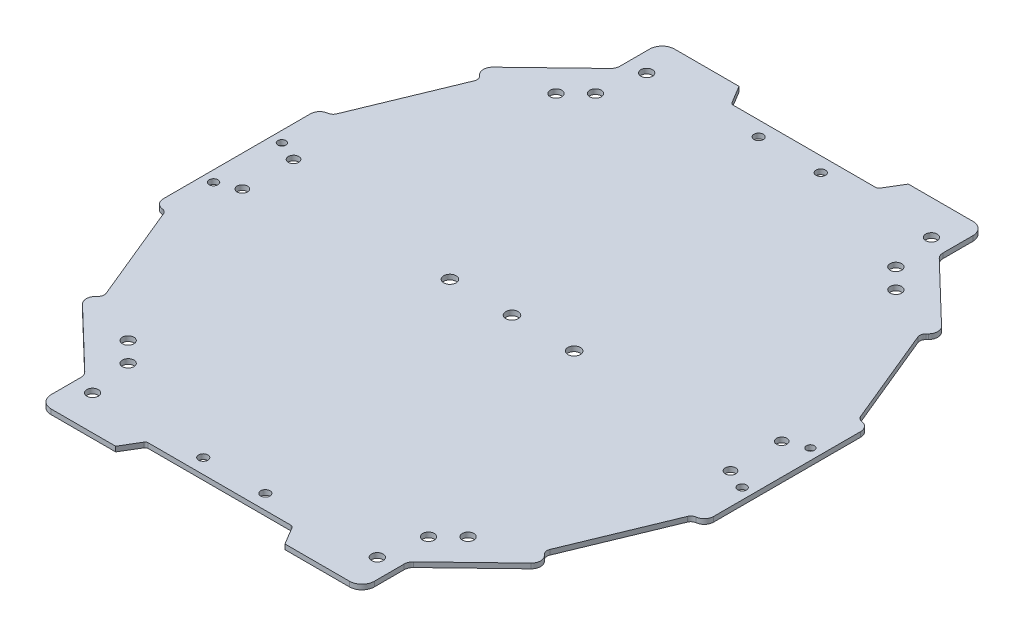
SolidWorks part; units mm, degrees
ref_plane "Front Plane" through (0, 0, 0) normal (0, 0, 1) x (1, 0, 0)
ref_plane "Top Plane" through (0, 0, 0) normal (0, 1, 0) x (1, 0, 0)
ref_plane "Right Plane" through (0, 0, 0) normal (1, 0, 0) x (0, 0, -1)
ref_plane "Plane1"
sketch "Sketch1" plane through (0, 0, 0) normal (0, 1, 0) x (-1, 0, 0)
  line L0 (74.0875, 321.0883) -> (70.3692, 327.2855)
  line L1 (70.3692, 327.2855) -> (45.5805, 327.2855)
  line L2 (45.5805, 327.2855) -> (45.5805, 312.4122)
  line L3 (45.5805, 312.4122) -> (23.246, 290.9343)
  line L4 (23.246, 290.9343) -> (26.6825, 287.3608)
  line L5 (26.6825, 287.3608) -> (12.7354, 253.539)
  line L6 (12.7354, 253.539) -> (9.0171, 253.539)
  line L7 (9.0171, 253.539) -> (9.0171, 226.8911)
  line L8 (9.0171, 226.8911) -> (9.0171, 200.2432)
  line L9 (9.0171, 200.2432) -> (12.7354, 200.2432)
  line L10 (12.7354, 200.2432) -> (26.6825, 166.4214)
  line L11 (26.6825, 166.4214) -> (23.246, 162.8479)
  line L12 (23.246, 162.8479) -> (45.5805, 141.37)
  line L13 (45.5805, 141.37) -> (45.5805, 126.4967)
  line L14 (45.5805, 126.4967) -> (70.3692, 126.4967)
  line L15 (70.3692, 126.4967) -> (74.0875, 132.6939)
  line L16 (74.0875, 132.6939) -> (97.6368, 132.6939)
  line L17 (97.6368, 132.6939) -> (121.1861, 132.6939)
  line L18 (121.1861, 132.6939) -> (124.9044, 126.4967)
  line L19 (124.9044, 126.4967) -> (149.6932, 126.4967)
  line L20 (149.6932, 126.4967) -> (149.6932, 141.37)
  line L21 (149.6932, 141.37) -> (172.0276, 162.8479)
  line L22 (172.0276, 162.8479) -> (168.5911, 166.4214)
  line L23 (168.5911, 166.4214) -> (182.5382, 200.2432)
  line L24 (182.5382, 200.2432) -> (186.2565, 200.2432)
  line L25 (186.2565, 200.2432) -> (186.2565, 226.8911)
  line L26 (186.2565, 226.8911) -> (186.2565, 253.539)
  line L27 (186.2565, 253.539) -> (182.5382, 253.539)
  line L28 (182.5382, 253.539) -> (168.5911, 287.3608)
  line L29 (168.5911, 287.3608) -> (172.0276, 290.9343)
  line L30 (172.0276, 290.9343) -> (149.6932, 312.4122)
  line L31 (149.6932, 312.4122) -> (149.6932, 327.2855)
  line L32 (149.6932, 327.2855) -> (124.9044, 327.2855)
  line L33 (124.9044, 327.2855) -> (121.1861, 321.0883)
  line L34 (121.1861, 321.0883) -> (97.6368, 321.0883)
  line L35 (97.6368, 321.0883) -> (74.0875, 321.0883)
  line L36 (97.6368, 132.6939) -> (97.6368, 321.0883) construction
  line L37 (9.0171, 226.8911) -> (186.2565, 226.8911) construction
  line L38 (67.6368, 256.8911) -> (127.6368, 196.8911) construction
  line L39 (127.6368, 256.8911) -> (67.6368, 196.8911) construction
  line L40 (42.8881, 295.782) -> (49.2662, 302.1601) construction
  line L41 (146.0075, 302.1601) -> (152.3856, 295.782) construction
  line L42 (49.2662, 151.6221) -> (42.8881, 158.0002) construction
  line L43 (146.0075, 151.6221) -> (152.3856, 158.0002) construction
  line L44 (12.5171, 237.8911) -> (12.5171, 215.8911) construction
  line L45 (19.0171, 218.6411) -> (19.0171, 235.1411) construction
  line L46 (107.6368, 316.3383) -> (87.6368, 316.3383) construction
  line L126 (176.3908, 226.8911) -> (176.3908, 225.1916)
  circle A1 centre (49.2662, 151.6221) radius 1.8592
  circle A5 centre (117.6368, 226.8911) radius 2
  circle A6 centre (77.6368, 226.8911) radius 2
  circle A7 centre (97.6368, 226.8911) radius 2
  circle A8 centre (12.5171, 215.8911) radius 1.2889
  circle A9 centre (12.5171, 237.8911) radius 1.4072
  circle A10 centre (107.6368, 316.3383) radius 1.5
  circle A11 centre (87.6368, 316.3383) radius 1.5
  circle A12 centre (87.6368, 137.4439) radius 1.5
  circle A13 centre (107.6368, 137.4439) radius 1.5
  circle A14 centre (182.7565, 215.8911) radius 1.2889
  circle A15 centre (182.7565, 237.8911) radius 1.4072
  circle A16 centre (176.2565, 235.1411) radius 1.6732
  circle A17 centre (176.2565, 218.6411) radius 1.6732
  circle A22 centre (51.7777, 316.1305) radius 1.8592
  circle A23 centre (49.2662, 302.1601) radius 1.8592
  circle A24 centre (19.0171, 235.1411) radius 1.6732
  circle A27 centre (143.496, 137.6517) radius 1.8592
  circle A28 centre (146.0075, 151.6221) radius 1.8592
  circle A30 centre (143.496, 316.1305) radius 1.8592
  circle A54 centre (146.0075, 302.1601) radius 1.8592
  circle A74 centre (19.0171, 218.6411) radius 1.6732
  circle A77 centre (51.7777, 137.6517) radius 1.8592
  circle A82 centre (42.8881, 158.0002) radius 1.8592
  circle A86 centre (152.3856, 295.782) radius 1.8592
  circle A87 centre (42.8881, 295.782) radius 1.8592
  circle A91 centre (152.3856, 158.0002) radius 1.8592
  point P36 (19.0171, 226.8911)
  point P43 (97.6368, 316.3383)
  point P56 (12.5171, 226.8911)
  dimension "D1" = 30
  dimension "D11" = 20
  dimension "D14" = 40
  dimension "D28" = 6.1972
  dimension "D2" = 30
  dimension "D3" = 30
  dimension "D4" = 30
  dimension "D5" = 10
  dimension "D6" = 16.5
  dimension "D7" = 30
  dimension "D8" = 30
  dimension "D9" = 30
  dimension "D10" = 30
  dimension "D12" = 4.75
  dimension "D15" = 20
  dimension "D16" = 9.02
  dimension "D17" = 9.02
  dimension "D18" = 9.02
  dimension "D19" = 9.02
  dimension "D20" = 10
  dimension "D21" = 10
  dimension "D22" = 10
  dimension "D23" = 10
  dimension "D24" = 45
  dimension "D25" = 45
  dimension "D26" = 45
  dimension "D27" = 45
  dimension "D29" = 3.5
  dimension "D30" = 22
extrude "Extrusion1" add sketch "Sketch1" along normal blind 1.6
fillet "Fillet1" radius 1 4 edges at (-121.1861, 0.8, 132.6939) (-74.0875, 0.8, 132.6939) (-74.0875, 0.8, 321.0883) (-121.1861, 0.8, 321.0883)
fillet "Fillet2" radius 4 4 edges at (-149.6932, 0.8, 126.4967) (-45.5805, 0.8, 126.4967) (-149.6932, 0.8, 327.2855) (-45.5805, 0.8, 327.2855)
fillet "Fillet3" radius 3 4 edges at (-149.6932, 0.8, 141.37) (-45.5805, 0.8, 141.37) (-45.5805, 0.8, 312.4122) (-149.6932, 0.8, 312.4122)
fillet "Fillet4" radius 3 1 edges at (-172.0276, 0.8, 290.9343)
fillet "Fillet5" radius 2 1 edges at (-168.5911, 0.8, 287.3608)
fillet "Fillet6" radius 2 1 edges at (-26.6825, 0.8, 287.3608)
fillet "Fillet7" radius 3 1 edges at (-23.246, 0.8, 290.9343)
fillet "Fillet8" radius 3 2 edges at (-172.0276, 0.8, 162.8479) (-23.246, 0.8, 162.8479)
fillet "Fillet9" radius 2 2 edges at (-26.6825, 0.8, 166.4214) (-168.5911, 0.8, 166.4214)
fillet "Fillet10" radius 2 4 edges at (-12.7354, 0.8, 200.2432) (-12.7354, 0.8, 253.539) (-182.5382, 0.8, 253.539) (-182.5382, 0.8, 200.2432)
fillet "Fillet11" radius 3 4 edges at (-186.2565, 0.8, 200.2432) (-186.2565, 0.8, 253.539) (-9.0171, 0.8, 253.539) (-9.0171, 0.8, 200.2432)
